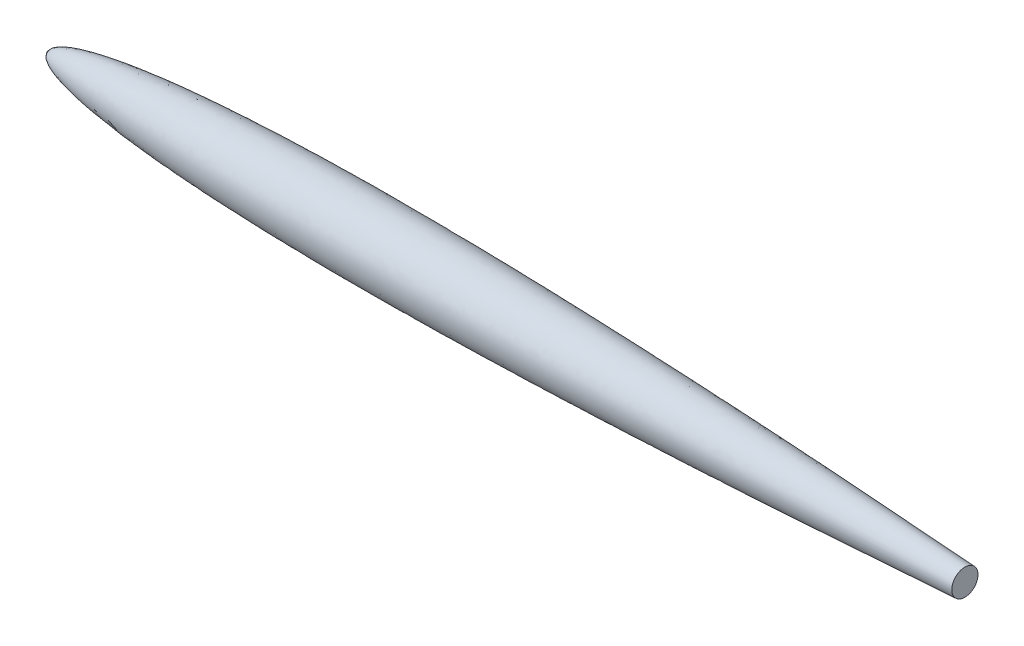
SolidWorks part; units mm, degrees
ref_plane "Front Plane" through (0, 0, 0) normal (0, 0, 1) x (1, 0, 0)
ref_plane "Top Plane" through (0, 0, 0) normal (0, 1, 0) x (1, 0, 0)
ref_plane "Right Plane" through (0, 0, 0) normal (1, 0, 0) x (0, 0, -1)
sketch "rootSketch" plane through (0, 0, 0) normal (0, 1, 0) x (1, 0, 0)
  line L0 (0, 0) -> (12000, 0) construction
  line L1 (2287.5, -274.5) -> (2287.5, 274.5) construction
  line L2 (0, 0) -> (9150, 0)
  spline S0 degree 4 poles (0, 0) (0.0002, 1.1783) (0.1019, 3.5275) (0.5605, 7.0328) (1.7549, 11.5943) (3.4354, 15.9) (5.4991, 19.934) (8.311, 24.4289) (11.4852, 28.5908) (14.9769, 32.5095) (19.9691, 37.4422) (26.9376, 43.4504) (36.0876, 50.0708) (47.4769, 57.0778) (61.5404, 64.6525) (77.1838, 72.0716) (94.7922, 79.4526) (114.338, 86.7678) (138.331, 94.9404) (167.4375, 103.839) (202.1902, 113.2976) (242.6189, 123.0791) (283.8524, 132.0744) (324.9149, 140.2471) (365.7664, 147.7384) (416.4511, 156.3658) (477.0221, 165.7669) (547.8456, 175.6689) (630.5882, 186.0011) (715.1014, 195.4737) (801.3628, 204.1819) (889.3556, 212.1992) (977.4135, 219.4631) (1065.524, 226.0562) (1153.6774, 232.0453) (1241.8663, 237.486) (1352.1845, 243.6614) (1484.6517, 250.1476) (1639.2816, 256.5129) (1816.0804, 262.345) (1992.9164, 266.8975) (2169.7779, 270.3041) (2346.6562, 272.6757) (2523.5444, 274.1064) (2744.6606, 274.8195) (3010.0013, 274.0955) (3319.5538, 271.2162) (3673.2968, 265.5239) (4026.9995, 257.745) (4380.6568, 248.1375) (4734.2663, 236.9143) (5087.8269, 224.2504) (5441.3385, 210.2884) (5794.8011, 195.1423) (6148.2151, 178.9004) (6501.5801, 161.6274) (6810.731, 145.6485) (7075.6854, 131.3482) (7296.4585, 119.0291) (7473.0634, 108.9317) (7649.6541, 98.5899) (7826.2302, 88.0006) (7980.7208, 78.5146) (8113.1314, 70.2227) (8223.4666, 63.2035) (8311.7306, 57.5217) (8399.99, 51.7724) (8488.2454, 45.9546) (8565.4639, 40.8032) (8631.6499, 36.3433) (8686.8001, 32.5972) (8730.924, 29.5818) (8775.0366, 26.5489) (8819.1658, 23.4963) (8863.2634, 20.4273) (8907.4107, 17.3359) (8951.4689, 14.232) (8990.1608, 11.4889) (9023.0969, 9.1423) (9050.9049, 7.1523) (9072.4988, 5.6029) (9095.4424, 3.9504) (9115.8352, 2.4783) (9143.0366, 0.5069) (9162.6518, -0.9192) (9195.0933, -3.2849) (9220.197, -5.1263) (9250.9065, -7.3837) (9278.2355, -9.4041) (9307.6056, -11.5815) (9335.7473, -13.6784) (9364.6143, -15.8368) (9393.0714, -17.9743) (9428.8949, -20.6757) (9471.7457, -23.9254) (9521.8197, -27.7492) (9578.9933, -32.1522) (9636.1916, -36.5945) (9693.3708, -41.0733) (9750.5568, -45.5912) (9807.7337, -50.1474) (9864.9111, -54.7434) (9922.083, -59.3791) (9979.2532, -64.0555) (10022.1272, -67.5936) (10050.7094, -69.9664) (10065, -71.1562) knots 0 0 0 0 0 0.000464 0.000929 0.001393 0.001858 0.002287 0.002716 0.003486 0.003922 0.004359 0.005488 0.007118 0.008378 0.009638 0.011797 0.013955 0.015919 0.017882 0.02181 0.025978 0.030146 0.034314 0.038482 0.042518 0.046554 0.054626 0.062698 0.07077 0.079497 0.088224 0.096952 0.105679 0.114406 0.123133 0.13186 0.140587 0.158059 0.17553 0.193002 0.210474 0.227946 0.245418 0.26289 0.280362 0.315306 0.35025 0.385194 0.420137 0.455081 0.490025 0.524969 0.559913 0.594857 0.6298 0.664744 0.699688 0.71716 0.734632 0.752104 0.769576 0.787048 0.80452 0.813256 0.821992 0.830728 0.839464 0.8482 0.856935 0.861303 0.865671 0.870039 0.874407 0.878775 0.883143 0.887511 0.891879 0.896247 0.898431 0.900615 0.902799 0.904983 0.907167 0.909351 0.912184 0.915017 0.91785 0.920682 0.923515 0.926348 0.929181 0.932013 0.934846 0.937679 0.943345 0.94901 0.954676 0.960341 0.966007 0.971672 0.977338 0.983003 0.988669 0.994334 1 1 1 1 1 construction
  spline S1 degree 4 poles (0, 0) (0.0002, 1.1783) (0.1019, 3.5275) (0.5605, 7.0328) (1.7549, 11.5943) (3.4354, 15.9) (5.4991, 19.934) (8.311, 24.4289) (11.4852, 28.5908) (14.9769, 32.5095) (19.9691, 37.4422) (26.9376, 43.4504) (36.0876, 50.0708) (47.4769, 57.0778) (61.5404, 64.6525) (77.1838, 72.0716) (94.7922, 79.4526) (114.338, 86.7678) (138.331, 94.9404) (167.4375, 103.839) (202.1902, 113.2976) (242.6189, 123.0791) (283.8524, 132.0744) (324.9149, 140.2471) (365.7664, 147.7384) (416.4511, 156.3658) (477.0221, 165.7669) (547.8456, 175.6689) (630.5882, 186.0011) (715.1014, 195.4737) (801.3628, 204.1819) (889.3556, 212.1992) (977.4135, 219.4631) (1065.524, 226.0562) (1153.6774, 232.0453) (1241.8663, 237.486) (1352.1845, 243.6614) (1484.6517, 250.1476) (1639.2816, 256.5129) (1816.0804, 262.345) (1992.9164, 266.8975) (2169.7779, 270.3041) (2346.6562, 272.6757) (2523.5444, 274.1064) (2744.6606, 274.8195) (3010.0013, 274.0955) (3319.5538, 271.2162) (3673.2968, 265.5239) (4026.9995, 257.745) (4380.6568, 248.1375) (4734.2663, 236.9143) (5087.8269, 224.2504) (5441.3385, 210.2884) (5794.8011, 195.1423) (6148.2151, 178.9004) (6501.5801, 161.6274) (6810.731, 145.6485) (7075.6854, 131.3482) (7296.4585, 119.0291) (7473.0634, 108.9317) (7649.6541, 98.5899) (7826.2302, 88.0006) (7980.7208, 78.5146) (8113.1314, 70.2227) (8223.4666, 63.2035) (8311.7306, 57.5217) (8399.99, 51.7724) (8488.2454, 45.9546) (8565.4639, 40.8032) (8631.6499, 36.3433) (8686.8001, 32.5972) (8730.924, 29.5818) (8775.0366, 26.5489) (8819.1658, 23.4963) (8863.2634, 20.4273) (8907.4107, 17.3359) (8951.4689, 14.232) (8990.1608, 11.4889) (9023.0969, 9.1423) (9050.9049, 7.1523) (9072.4988, 5.6029) (9095.4424, 3.9504) (9115.8352, 2.4783) (9134.8259, 1.1019) (9144.9864, 0.3644) (9150, 0) knots 0 0 0 0 0 0.000464 0.000929 0.001393 0.001858 0.002287 0.002716 0.003486 0.003922 0.004359 0.005488 0.007118 0.008378 0.009638 0.011797 0.013955 0.015919 0.017882 0.02181 0.025978 0.030146 0.034314 0.038482 0.042518 0.046554 0.054626 0.062698 0.07077 0.079497 0.088224 0.096952 0.105679 0.114406 0.123133 0.13186 0.140587 0.158059 0.17553 0.193002 0.210474 0.227946 0.245418 0.26289 0.280362 0.315306 0.35025 0.385194 0.420137 0.455081 0.490025 0.524969 0.559913 0.594857 0.6298 0.664744 0.699688 0.71716 0.734632 0.752104 0.769576 0.787048 0.80452 0.813256 0.821992 0.830728 0.839464 0.8482 0.856935 0.861303 0.865671 0.870039 0.874407 0.878775 0.883143 0.887511 0.891879 0.896247 0.898431 0.900615 0.902799 0.904983 0.907167 0.909351 0.909351 0.909351 0.909351 0.909351
  point P5 (2287.5, 0)
  dimension "rootQuarterChord" = 2287.5
  dimension "rootMaxThickness" = 549
revolve "Revolve1" add sketch "rootSketch" angle 360 about L0
ref_plane "Plane1" through (7503, 0, 0) normal (1, 0, 0) x (0, 0, -1)
sketch "cutSketch" plane through (7503, 0, 0) normal (1, 0, 0) x (0, 0, -1)
  circle A0 centre (0, 0) radius 274.5
  dimension "cutDiameter" = 549
extrude "Cut-Extrude1" cut sketch "cutSketch" along normal through all
equation "\"chord\"= 9.15"
equation "\"NACAairfoil\"= 0006"
equation "\"tailCutoffPercentage\"= 0.18"
equation "\"rootQuarterChord@rootSketch\"=\"chord\"/4"
equation "\"rootMaxThickness@rootSketch\"= \"rootQuarterChord@rootSketch\" * 4 * \"NACAairfoil\" / 100"
equation "\"cutDiameter@cutSketch\"=\"rootMaxThickness@rootSketch\""
equation "\"cutChord@Plane1\"= \"rootQuarterChord@rootSketch\" * 4 * ( 1 - \"tailCutoffPercentage\" )"
